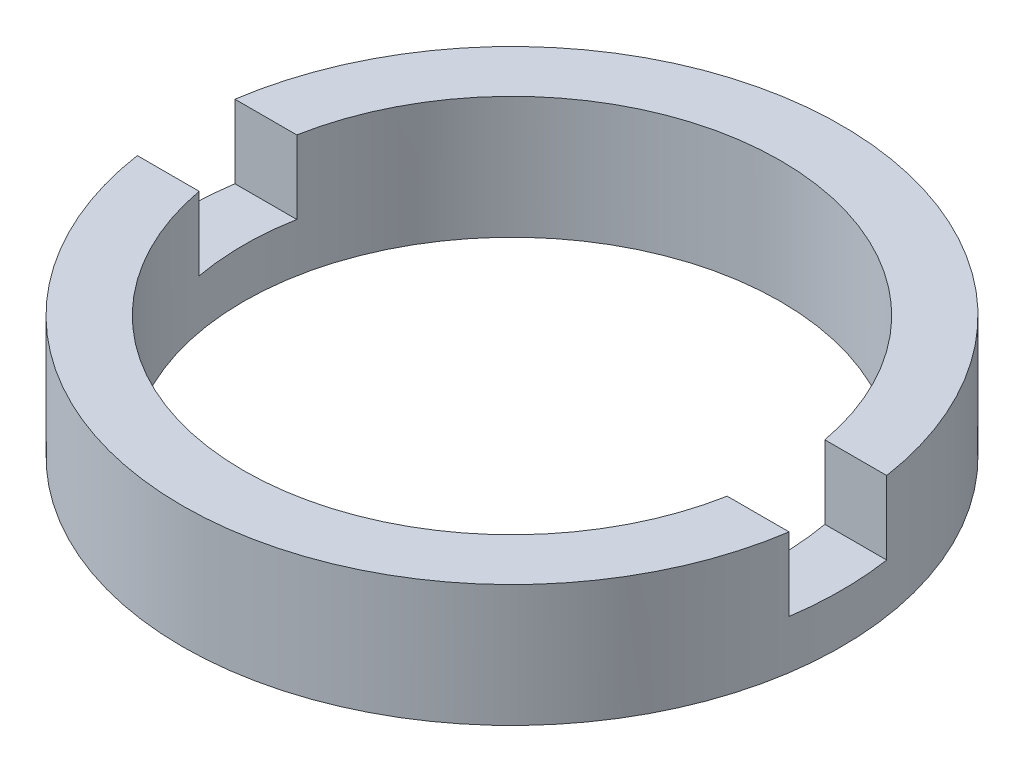
SolidWorks part; units mm, degrees
ref_plane "前视基准面" through (0, 0, 0) normal (0, 0, 1) x (1, 0, 0)
ref_plane "上视基准面" through (0, 0, 0) normal (0, 1, 0) x (1, 0, 0)
ref_plane "右视基准面" through (0, 0, 0) normal (1, 0, 0) x (0, 0, -1)
sketch "草图1" plane through (0, 0, 0) normal (0, 0, 1) x (1, 0, 0)
  line L0 (0, 56.2608) -> (0, -99.1922) construction
  line L1 (5.5, -1.9642) -> (6.75, -1.9642)
  line L4 (6.75, -1.9642) -> (6.75, -4.4642)
  line L5 (5.5, -4.4642) -> (5.5, -1.9642)
  line L7 (5.5, -4.4642) -> (6.75, -4.4642)
  dimension "D1" = 2.5
  dimension "D2" = 6.75
  dimension "D3" = 5.5
revolve "旋转1" add sketch "草图1" angle 360 about L0
cosmetic thread "装饰螺纹线1"
sketch "草图2" plane through (0, -1.9642, 0) normal (0, 1, 0) x (1, 0, 0)
  line L0 (-28.67, 0) -> (29.9422, 0) construction
  line L2 (-26.8525, 1) -> (26.8525, 1)
  line L3 (-26.8525, 1) -> (-26.8525, -1)
  line L4 (-26.8525, -1) -> (26.8525, -1)
  line L5 (26.8525, 1) -> (26.8525, -1)
  line L6 (-26.8525, 1) -> (26.8525, -1) construction
  line L7 (-26.8525, -1) -> (26.8525, 1) construction
  point P3 (0, 0)
  dimension "D1" = 2
extrude "切除-拉伸1" cut sketch "草图2" against normal blind 1.5
